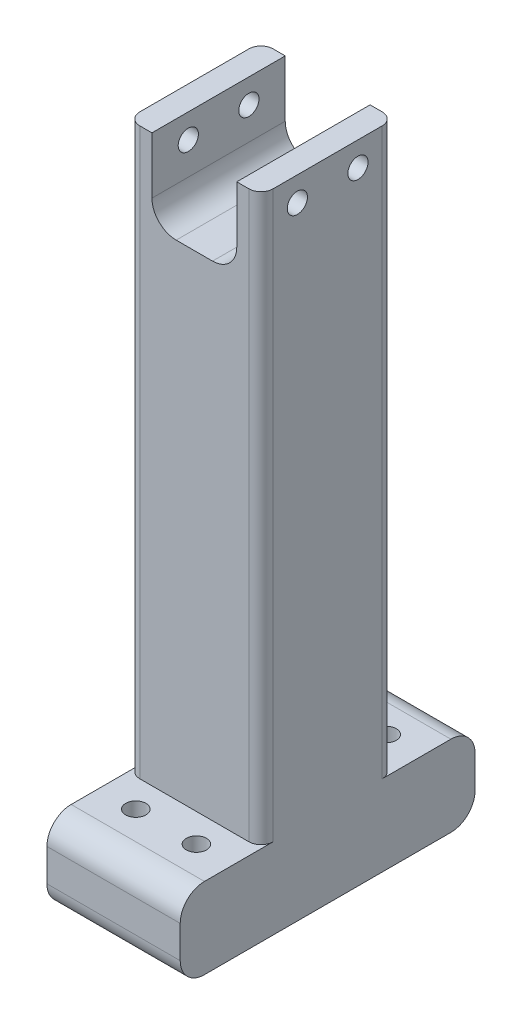
SolidWorks part; units mm, degrees
ref_plane "Front Plane" through (0, 0, 0) normal (0, 0, 1) x (1, 0, 0)
ref_plane "Top Plane" through (0, 0, 0) normal (0, 1, 0) x (1, 0, 0)
ref_plane "Right Plane" through (0, 0, 0) normal (1, 0, 0) x (0, 0, -1)
sketch "Sketch1" plane through (0, 0, 0) normal (0, 1, 0) x (1, 0, 0)
  line L0 (0, 9.525) -> (0, -9.525) construction
  line L5 (9.525, 0) -> (-9.525, 0) construction
  line L9 (-13.335, -13.335) -> (13.335, -13.335)
  line L10 (-13.335, -13.335) -> (-13.335, 13.335)
  line L11 (-13.335, 13.335) -> (13.335, 13.335)
  line L12 (13.335, -13.335) -> (13.335, 13.335)
  point P4 (-13.335, 0)
  point P6 (0, -13.335)
  point P11 (0, 0)
  point P12 (0, 0)
  dimension "D1" = 26.67
  dimension "D2" = 26.67
  dimension "D3" = 19.05
  dimension "D4" = 19.05
extrude "Boss-Extrude1" add sketch "Sketch1" along normal blind 5.08
sketch "Sketch9" plane through (0, 0, 0) normal (0, -1, 0) x (1, 0, 0)
  line L22 (20.955, -20.955) -> (20.955, 20.955)
  line L27 (-20.955, 20.955) -> (20.955, 20.955)
  line L28 (-20.955, -20.955) -> (-20.955, 20.955)
  line L29 (-20.955, -20.955) -> (20.955, -20.955)
  point P0 (-20.955, 0)
  point P1 (0, 20.955)
  dimension "D1" = 41.91
  dimension "D2" = 41.91
extrude "Boss-Extrude7" add sketch "Sketch9" against normal blind 203.2
sketch "Sketch10" plane through (0, 0, 20.955) normal (0, 0, 1) x (1, 0, 0)
  line L0 (-13.335, 185.42) -> (-13.335, 203.2)
  line L1 (20.955, 203.2) -> (-20.955, 203.2) construction
  line L2 (-13.335, 203.2) -> (13.335, 203.2)
  line L3 (13.335, 203.2) -> (13.335, 185.42)
  line L4 (5.715, 177.8) -> (-5.715, 177.8)
  arc A0 (13.335, 185.42) -> (5.715, 177.8) centre (5.715, 185.42) cw
  arc A1 (-13.335, 185.42) -> (-5.715, 177.8) centre (-5.715, 185.42) ccw
  point P10 (0, 203.2)
  point P11 (0, 203.2)
  dimension "D1" = 7.62
  dimension "D2" = 26.67
  dimension "D3" = 25.4
extrude "Cut-Extrude4" cut sketch "Sketch10" against normal through all
sketch "Sketch11" plane through (-20.955, 0, 0) normal (-1, 0, 0) x (0, 0, 1)
  line L0 (-9.525, 195.58) -> (9.525, 195.58) construction
  line L1 (20.955, 203.2) -> (-20.955, 203.2) construction
  circle A0 centre (-9.525, 195.58) radius 3.175
  circle A1 centre (9.525, 195.58) radius 3.175
  point P4 (0, 195.58)
  point P7 (0, 203.2)
  dimension "D1" = 6.35
  dimension "D2" = 19.05
  dimension "D3" = 17.78
extrude "Cut-Extrude5" cut sketch "Sketch11" against normal through all
sketch "Sketch12" plane through (0, 0, 20.955) normal (0, 0, 1) x (1, 0, 0)
  line L0 (20.955, 0) -> (-20.955, 0) construction
  line L2 (-20.955, 0) -> (20.955, 0)
  line L3 (-20.955, 0) -> (-20.955, 25.4)
  line L4 (-20.955, 25.4) -> (20.955, 25.4)
  line L5 (20.955, 0) -> (20.955, 25.4)
  point P6 (0, 0)
  point P7 (0, 0)
  dimension "D1" = 25.4
  dimension "D2" = 41.91
extrude "Boss-Extrude8" add sketch "Sketch12" along normal blind 25.4
sketch "Sketch13" plane through (0, 25.4, 0) normal (0, 1, 0) x (1, 0, 0)
  line L0 (9.525, -29.845) -> (-9.525, -29.845) construction
  line L1 (20.955, -46.355) -> (-20.955, -46.355) construction
  circle A0 centre (-9.525, -29.845) radius 3.175
  circle A1 centre (9.525, -29.845) radius 3.175
  point P4 (0, -29.845)
  dimension "D2" = 6.35
  dimension "D1" = 16.51
  dimension "D3" = 19.05
extrude "Cut-Extrude6" cut sketch "Sketch13" against normal through all
mirror "Mirror1" about plane through (0, 0, 0) normal (0, 0, 1) of "Cut-Extrude6", "Boss-Extrude8"
fillet "Fillet2" radius 3.81 4 edges at (20.955, 114.3, -20.955) (20.955, 114.3, 20.955) (-20.955, 114.3, -20.955) (-20.955, 114.3, 20.955)
fillet "Fillet3" radius 7.62 4 edges at (0, 25.4, -46.355) (0, 0, -46.355) (0, 0, 46.355) (0, 25.4, 46.355)
